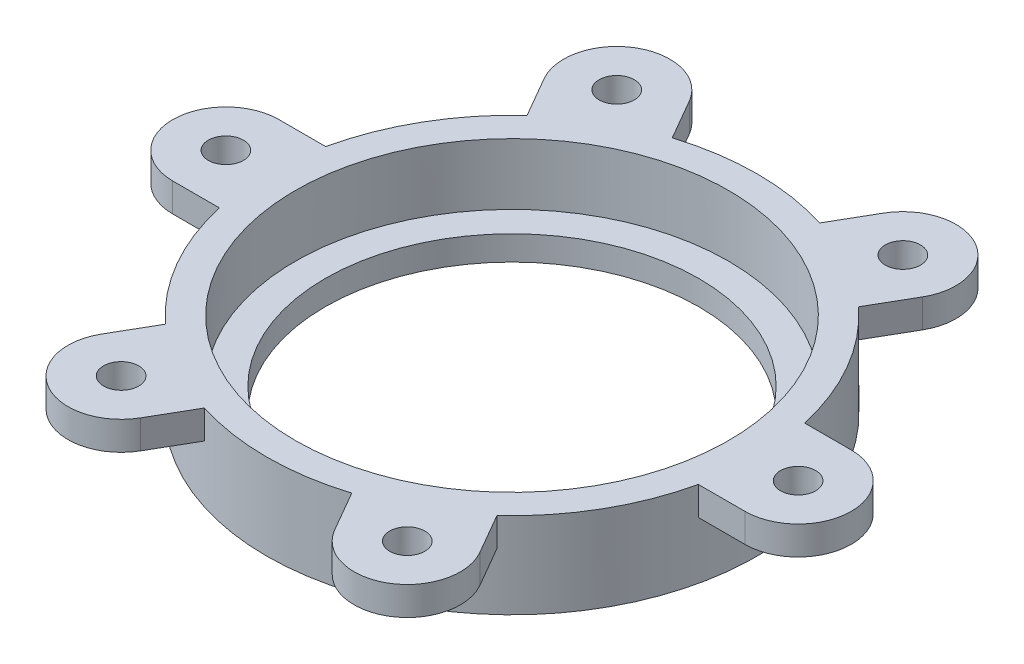
SolidWorks part; units mm, degrees
ref_plane "Front Plane" through (0, 0, 0) normal (0, 0, 1) x (1, 0, 0)
ref_plane "Top Plane" through (0, 0, 0) normal (0, 1, 0) x (1, 0, 0)
ref_plane "Right Plane" through (0, 0, 0) normal (1, 0, 0) x (0, 0, -1)
sketch "Sketch1" plane through (0, 0, 0) normal (0, 1, 0) x (1, 0, 0)
  line L0 (11.8708, -33.5609) -> (9.0145, -28.6136)
  line L1 (23.1292, -27.0609) -> (20.2728, -22.1136)
  line L2 (35, 6.5) -> (29.2874, 6.5)
  line L3 (-23.1292, -27.0609) -> (-20.2728, -22.1136)
  line L4 (35, -6.5) -> (29.2874, -6.5)
  line L5 (-11.8708, -33.5609) -> (-9.0145, -28.6136)
  line L6 (-35, 6.5) -> (-29.2874, 6.5)
  line L7 (-35, -6.5) -> (-29.2874, -6.5)
  line L8 (-11.8708, 33.5609) -> (-9.0145, 28.6136)
  line L9 (-23.1292, 27.0609) -> (-20.2728, 22.1136)
  line L10 (23.1292, 27.0609) -> (20.2728, 22.1136)
  line L11 (11.8708, 33.5609) -> (9.0145, 28.6136)
  arc A0 (29.2874, 6.5) -> (20.2728, 22.1136) centre (0, 0) ccw
  circle A1 centre (0, 0) radius 26
  circle A2 centre (35, 0) radius 2.15
  arc A3 (35, -6.5) -> (35, 6.5) centre (35, 0) ccw
  arc A4 (11.8708, -33.5609) -> (23.1292, -27.0609) centre (17.5, -30.3109) ccw
  circle A5 centre (17.5, -30.3109) radius 2.15
  arc A6 (-23.1292, -27.0609) -> (-11.8708, -33.5609) centre (-17.5, -30.3109) ccw
  circle A7 centre (-17.5, -30.3109) radius 2.15
  arc A8 (-35, 6.5) -> (-35, -6.5) centre (-35, 0) ccw
  circle A9 centre (-35, 0) radius 2.15
  arc A10 (-11.8708, 33.5609) -> (-23.1292, 27.0609) centre (-17.5, 30.3109) ccw
  circle A11 centre (-17.5, 30.3109) radius 2.15
  arc A12 (23.1292, 27.0609) -> (11.8708, 33.5609) centre (17.5, 30.3109) ccw
  circle A13 centre (17.5, 30.3109) radius 2.15
  arc A14 (-20.2728, 22.1136) -> (-29.2874, 6.5) centre (0, 0) ccw
  arc A15 (9.0145, 28.6136) -> (-9.0145, 28.6136) centre (0, 0) ccw
  arc A16 (-29.2874, -6.5) -> (-20.2728, -22.1136) centre (0, 0) ccw
  arc A17 (-9.0145, -28.6136) -> (9.0145, -28.6136) centre (0, 0) ccw
  arc A18 (20.2728, -22.1136) -> (29.2874, -6.5) centre (0, 0) ccw
  point P41 (0, 0)
  dimension "D1" = 6
extrude "Boss-Extrude1" add sketch "Sketch1" along normal blind 10.5
sketch "Sketch2" plane through (0, 0, 0) normal (0, -1, 0) x (1, 0, 0)
  circle A0 centre (0, 0) radius 27.4489
  circle A1 centre (0, 0) radius 22.85
extrude "Boss-Extrude2" add sketch "Sketch2" against normal blind 3
sketch "Sketch3" plane through (0, 0, 0) normal (0, -1, 0) x (1, 0, 0)
  circle A0 centre (0, 0) radius 30
  circle A1 centre (0, 0) radius 44.0948
extrude "Cut-Extrude1" cut sketch "Sketch3" against normal blind 7
sketch "Sketch4" plane through (0, 10.5, 0) normal (0, 1, 0) x (1, 0, 0)
  circle A0 centre (0, 0) radius 26.5
extrude "Cut-Extrude2" cut sketch "Sketch4" against normal up to surface (7.5 mm away) up to face at (0, 3, -22.85)
